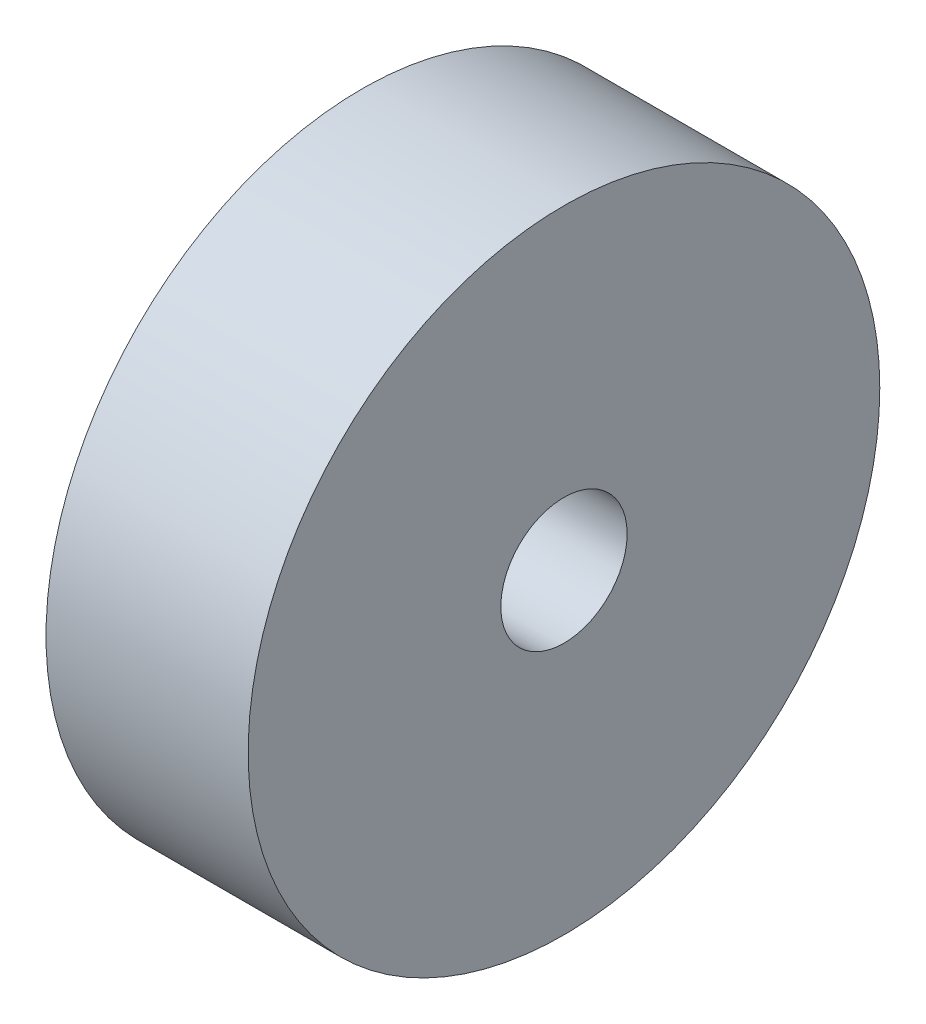
SolidWorks part; units mm, degrees
ref_plane "Front Plane" through (0, 0, 0) normal (0, 0, 1) x (1, 0, 0)
ref_plane "Top Plane" through (0, 0, 0) normal (0, 1, 0) x (1, 0, 0)
ref_plane "Right Plane" through (0, 0, 0) normal (1, 0, 0) x (0, 0, -1)
sketch "Sketch2" plane through (0, 0, 0) normal (1, 0, 0) x (0, 0, -1)
  circle A0 centre (0, 0) radius 12.5
  circle A1 centre (0, 0) radius 2.5
  dimension "D1" = 25
  dimension "D2" = 5
extrude "Boss-Extrude1" add sketch "Sketch2" along normal blind 8
